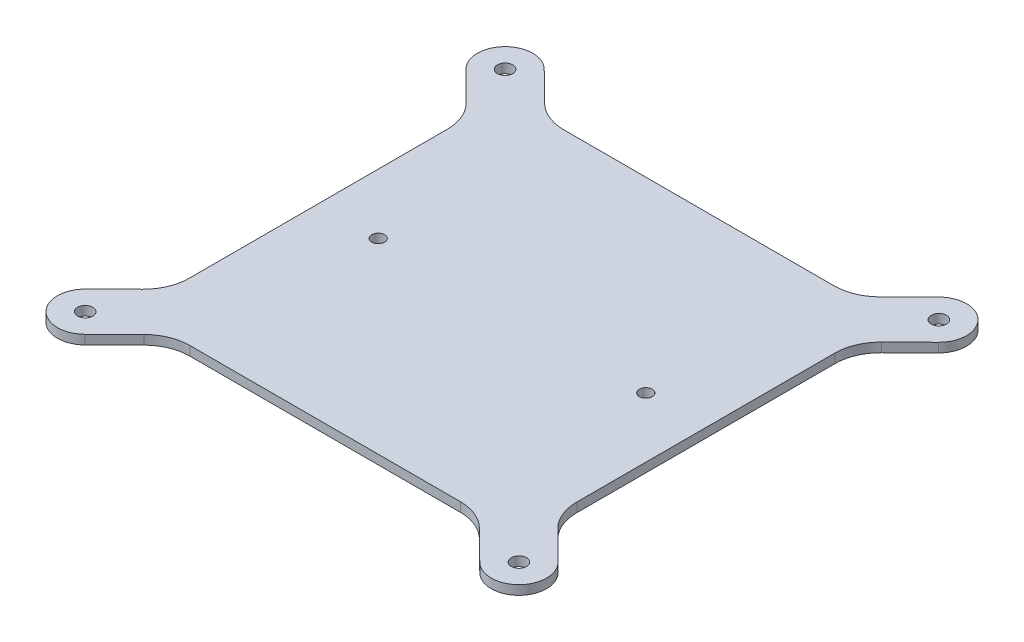
SolidWorks part; units mm, degrees
ref_plane "Front Plane" through (0, 0, 0) normal (0, 0, 1) x (1, 0, 0)
ref_plane "Top Plane" through (0, 0, 0) normal (0, 1, 0) x (1, 0, 0)
ref_plane "Right Plane" through (0, 0, 0) normal (1, 0, 0) x (0, 0, -1)
sketch "Sketch1" plane through (0, 0, 0) normal (0, 1, 0) x (1, 0, 0)
  line L0 (42, 40.5) -> (-42, 40.5)
  line L1 (40, -38.5) -> (-40, -38.5) construction
  line L2 (40, -38.5) -> (40, 38.5) construction
  line L3 (40, 38.5) -> (-40, 38.5) construction
  line L4 (-40, -38.5) -> (-40, 38.5) construction
  line L5 (40, -38.5) -> (-40, 38.5) construction
  line L6 (40, 38.5) -> (-40, -38.5) construction
  line L7 (47, -45.5) -> (-47, -45.5) construction
  line L8 (47, -45.5) -> (47, 45.5) construction
  line L9 (47, 45.5) -> (-47, 45.5) construction
  line L10 (-47, -45.5) -> (-47, 45.5) construction
  line L11 (47, -45.5) -> (-47, 45.5) construction
  line L12 (47, 45.5) -> (-47, -45.5) construction
  line L13 (-42, -40.5) -> (-42, 40.5)
  line L14 (42, -40.5) -> (-42, -40.5)
  line L15 (42, -40.5) -> (42, 40.5)
  point P0 (0, 0)
  point P6 (0, 0)
  dimension "D1" = 94
  dimension "D2" = 91
  dimension "D3" = 80
  dimension "D4" = 77
  dimension "D5" = 2
extrude "Boss-Extrude1" add sketch "Sketch1" along normal blind 2
sketch "Sketch2" plane through (0, 2, 0) normal (0, 1, 0) x (1, 0, 0)
  line L0 (-47, 45.5) -> (-37, 35.6125) construction
  line L1 (40, -38.5) -> (-40, 38.5) construction
  line L2 (-42.7814, 49.7666) -> (-32.7814, 39.8791)
  line L3 (-51.2186, 41.2334) -> (-41.2186, 31.3459)
  line L4 (-42, -40.5) -> (-42, 40.5) construction
  arc A0 (-42.7814, 49.7666) -> (-51.2186, 41.2334) centre (-47, 45.5) ccw
  arc A1 (-41.2186, 31.3459) -> (-32.7814, 39.8791) centre (-37, 35.6125) ccw
  circle A2 centre (-47, 45.5) radius 1.65
  point P5 (-42, 40.5563)
  dimension "6" = 6
  dimension "D2" = 3.3
extrude "Boss-Extrude2" add sketch "Sketch2" against normal up to surface (2 mm away) up to face at (0, 0, 0)
mirror "Mirror1" about plane through (0, 0, 0) normal (0, 0, 1) of "Boss-Extrude2"
mirror "Mirror2" about plane through (0, 0, 0) normal (1, 0, 0) of "Boss-Extrude2", "Mirror1"
fillet "Fillet1" radius 10 8 edges at (-42, 1, -32.1186) (-33.4094, 1, -40.5) (-42, 1, 32.1186) (-33.4094, 1, 40.5) (33.4094, 1, 40.5) (42, 1, 32.1186) (42, 1, -32.1186) (33.4094, 1, -40.5)
sketch "Sketch3" plane through (0, 2, 0) normal (0, 1, 0) x (1, 0, 0)
  line L0 (0, 0) -> (29, 0) construction
  line L3 (40, -38.5) -> (-40, 38.5) construction
  line L4 (-29, 0) -> (0, 0) construction
  circle A0 centre (-29, 0) radius 1.4
  circle A1 centre (29, 0) radius 1.4
  dimension "D2" = 2.8
  dimension "D1" = 58
extrude "Cut-Extrude1" cut sketch "Sketch3" against normal through all
